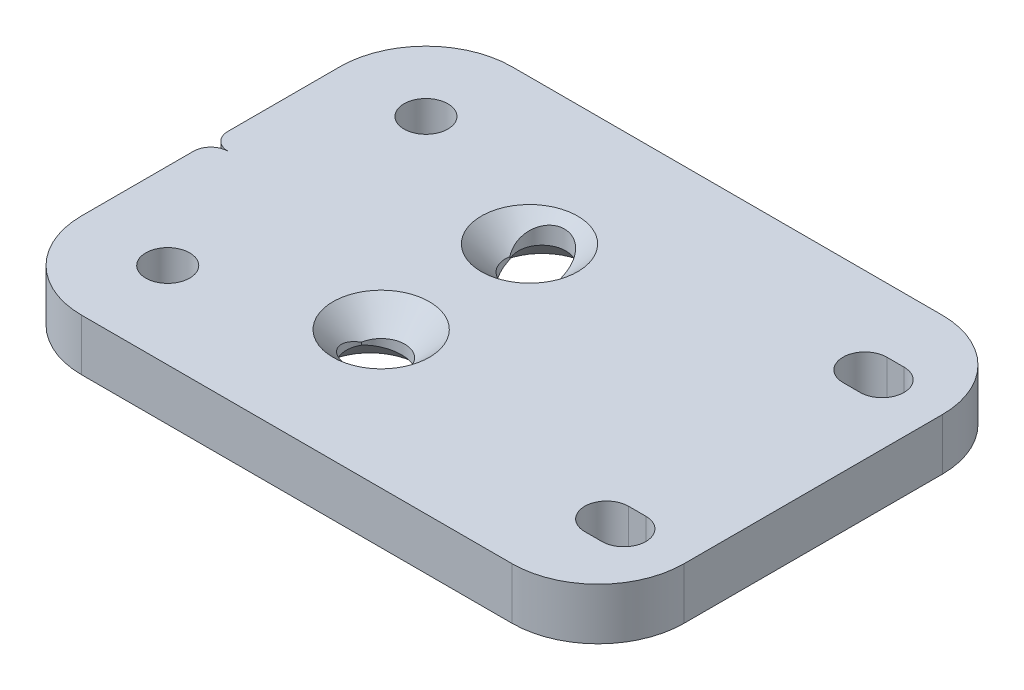
SolidWorks part; units mm, degrees
material "Клен"
ref_plane "Спереди" through (0, 0, 0) normal (0, 0, 1) x (1, 0, 0)
ref_plane "Сверху" through (0, 0, 0) normal (0, 1, 0) x (1, 0, 0)
ref_plane "Справа" through (0, 0, 0) normal (1, 0, 0) x (0, 0, -1)
sketch "Эскиз1" plane through (0, 0, 0) normal (0, 1, 0) x (1, 0, 0)
  line L0 (-41.181, -0.0464) -> (44.1026, -0.0464) construction
  line L10 (-25, -25) -> (25, -25)
  line L11 (-35, -15) -> (-35, 15)
  line L12 (-25, 25) -> (25, 25)
  line L13 (35, -15) -> (35, 15)
  line L14 (-35, -25) -> (35, 25) construction
  line L15 (-35, 25) -> (35, -25) construction
  arc A4 (25, 25) -> (35, 15) centre (25, 15) cw
  arc A5 (25, -25) -> (35, -15) centre (25, -15) ccw
  arc A6 (-25, -25) -> (-35, -15) centre (-25, -15) cw
  arc A7 (-35, 15) -> (-25, 25) centre (-25, 15) cw
  point P0 (0, 0)
  dimension "D1" = 10
  dimension "D2" = 50
  dimension "D3" = 70
extrude "Бобышка-Вытянуть1" add sketch "Эскиз1" along normal blind 6
sketch "Эскиз2" plane through (0, 0, 0) normal (0, -1, 0) x (1, 0, 0)
  line L0 (0, -37.0349) -> (0, 29.2907) construction
  line L1 (28, -15) -> (26, -15) construction
  line L2 (28, -17.55) -> (26, -17.55)
  line L3 (28, -12.45) -> (26, -12.45)
  line L6 (-46.1924, 0) -> (55.6646, 0) construction
  line L7 (28, 15) -> (26, 15) construction
  line L8 (28, 17.55) -> (26, 17.55)
  line L9 (28, 12.45) -> (26, 12.45)
  line L10 (-35, -15) -> (-35, 15) construction
  line L11 (25, -25) -> (-25, -25) construction
  circle A0 centre (-25, -15) radius 2.55
  arc A1 (28, -17.55) -> (28, -12.45) centre (28, -15) ccw
  arc A2 (26, -12.45) -> (26, -17.55) centre (26, -15) ccw
  arc A3 (28, 17.55) -> (28, 12.45) centre (28, 15) cw
  arc A4 (26, 12.45) -> (26, 17.55) centre (26, 15) cw
  circle A5 centre (-25, 15) radius 2.55
  point P7 (27, -15)
  point P12 (27, -17.55)
  point P21 (27, 15)
  dimension "D1" = 5.1
  dimension "D2" = 5.1
  dimension "D3" = 2
  dimension "D4" = 53
  dimension "D5" = 10
  dimension "D6" = 10
extrude "Вырез-Вытянуть1" cut sketch "Эскиз2" against normal through all
sketch "Эскиз3" plane through (0, 0, 0) normal (0, -1, 0) x (1, 0, 0)
  line L0 (-33, 0) -> (27.7687, 0) construction
  line L1 (-35, -15) -> (-35, 15) construction
  line L2 (-35, -2) -> (-35, 2)
  arc A0 (-33, 0) -> (-35, -2) centre (-33, -2) ccw
  arc A1 (-33, 0) -> (-35, 2) centre (-33, 2) cw
  point P3 (-35, -2)
  point P4 (-33, 0)
  point P7 (-35, 2)
  dimension "D2" = 2
  dimension "D1" = 2
extrude "Вырез-Вытянуть2" cut sketch "Эскиз3" against normal through all
hole_wizard "Зенковка для  винта с потайной головкой с внутренним шестигранником M52" positions "Эскиз6" profile "Эскиз7" countersink size "M5" standard "Ansi Metric" end condition through all
sketch "Эскиз6" plane through (0, 6, 0) normal (0, 1, 0) x (1, 0, 0)
  point P0 (-6.1594, -9.0403)
  point P2 (-6.1594, 8.1926)
sketch "Эскиз7" plane through (-6.1594, 6, 9.0403) normal (1, 0, 0) x (0, 0, 1)
  line L0 (0, 0) -> (0, 6)
  line L1 (0, 6) -> (2.75, 6)
  line L2 (2.75, 6) -> (2.75, 2.85)
  line L3 (2.75, 2.85) -> (5.6, 0)
  line L5 (5.6, 0) -> (0, 0)
  line L6 (-2.75, 2.85) -> (-5.6, 0) construction
  line L11 (0, -6.35) -> (0, 107.95) construction
  dimension "Диаметр сквозного отверстия" = 5.5
  dimension "Глубина сквозного отверстия" = 6
  dimension "Диаметр передней зенковки" = 11.2
  dimension "Угол передней зенковки" = 90
hole_wizard "Зенковка для  винта с потайной головкой с внутренним шестигранником M51" positions "Эскиз4" profile "Эскиз5" countersink size "M5" standard "Ansi Metric" end condition through all
sketch "Эскиз4" plane through (0, 0, 0) normal (0, -1, 0) x (-1, 0, 0)
  line L0 (0, -31.2686) -> (0, 36.0886) construction
  line L2 (42.0205, 0) -> (-55.2516, 0) construction
  point P0 (6.5, -10)
  point P2 (6.5, 10)
  point P22 (6.5, -10)
  point P24 (6.5, 10)
  point P28 (6.5, -10)
  point P30 (6.5, 10)
  dimension "D1" = 6.5
  dimension "D2" = 6.5
  dimension "D3" = 10
  dimension "D4" = 10
sketch "Эскиз5" plane through (-6.5, 0, 10) normal (1, 0, 0) x (0, 0, -1)
  line L0 (0, 0) -> (0, 6)
  line L1 (0, 6) -> (2.75, 6)
  line L2 (2.75, 6) -> (2.75, 2.85)
  line L3 (2.75, 2.85) -> (5.6, 0)
  line L5 (5.6, 0) -> (0, 0)
  line L6 (-2.75, 2.85) -> (-5.6, 0) construction
  line L11 (0, -6.35) -> (0, 107.95) construction
  dimension "Диаметр сквозного отверстия" = 5.5
  dimension "Глубина сквозного отверстия" = 6
  dimension "Диаметр передней зенковки" = 11.2
  dimension "Угол передней зенковки" = 90
equation "\"D2@Эскиз2\"=\"D1@Эскиз2\""
equation "\"D2@Эскиз4\"=\"D1@Эскиз4\""
equation "\"D4@Эскиз4\"=\"D3@Эскиз4\""
